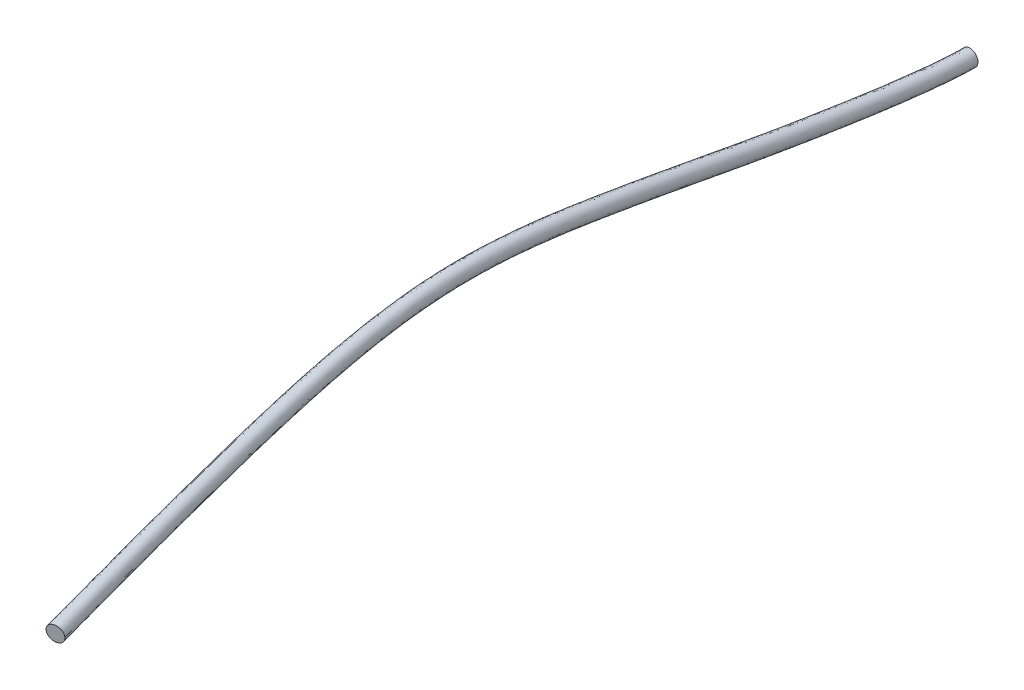
SolidWorks part; units mm, degrees
ref_plane "Front" through (0, 0, 0) normal (0, 0, 1) x (1, 0, 0)
ref_plane "Top" through (0, 0, 0) normal (0, 1, 0) x (1, 0, 0)
ref_plane "Right" through (0, 0, 0) normal (1, 0, 0) x (0, 0, -1)
sketch "Sketch1" plane through (0, 0, 0) normal (0, 0, 1) x (1, 0, 0)
  line L0 (0, 1.15) -> (0, -1.15) construction
  line L2 (1.15, 0) -> (0, 0) construction
  circle A0 centre (0, 0) radius 1.15
  dimension "D1" = 2.3
sketch3d "3DSketch1"
  line L1 (0, 0, 0) -> (0, 0, 5.3857) construction
  line L2 (0, 1.15, 0) -> (0, -1.15, 0) construction
  line L3 (1.15, 0, 0) -> (0, 0, 0) construction
  spline S0 degree 3 poles (0, 0, 0) (0, 0, 5.5543) (-1.7612, 1.9321, 28.7839) (-2.8099, 4.3303, 43.9339) (-5.1892, 6.756, 74.4946) (-1.8658, 2.7901, 99.9052) (4.6065, -1.3306, 134.516) knots 0 0 0 0 0.255985 0.525952 0.698297 1 1 1 1
  point P8 (0.3071, 0, 5.3769)
  point P13 (15.8194, 21.4659, 15.4797)
  point P14 (5.8044, 19.57, 2.1232)
  point P15 (24.4879, 44.2502, 3.6698)
  point P16 (5.8044, 0.7981, 17.2815)
  point P17 (24.4879, 0.9194, 42.5158)
  point P18 (22.8402, 3.2245, 59.1365)
  point P19 (33.7935, 2.6587, 73.3832)
  point P20 (39.2002, 2.6587, 91.2025)
  point P21 (0.7007, 0.7981, 18.1649)
  point P22 (1.2227, 0.9194, 42.0029)
  point P23 (2.7887, 3.2245, 59.0549)
  point P24 (1.5707, 2.6587, 74.7149)
  point P25 (-0.5173, 2.6587, 98.3789)
  point P26 (0, 0, 0)
  point P27 (-0.4619, 2.2326, 41.7659)
  point P28 (-1.025, 0.7967, 63.5251)
  point P29 (-1.1683, 4.7916, 63.1869)
  point P30 (-3.4843, 4.2151, 62.9582)
  point P31 (-2.3734, 1.8809, 41.4403)
  point P32 (-4.7794, 1.1704, 75.5217)
  point P33 (0, 0, 0)
  point P34 (0, 0, 0)
  point P35 (0, 0, 0)
  point P36 (1.7425, 4.0153, 76.0404)
  point P37 (0, 0, 0)
  point P38 (-4.3312, 5.0643, 70.0886)
  point P39 (-1.0066, 3.1688, 27.3629)
  point P40 (-2.7964, 6.3447, 50.1988)
  point P41 (-4.2122, 2.4667, 25.0174)
  point P42 (-2.0655, 1.8457, 25.3851)
  point P43 (3.0639, -5.1223, 96.5547)
sweep "Sweep1" add profiles "Sketch1" path "3DSketch1"
